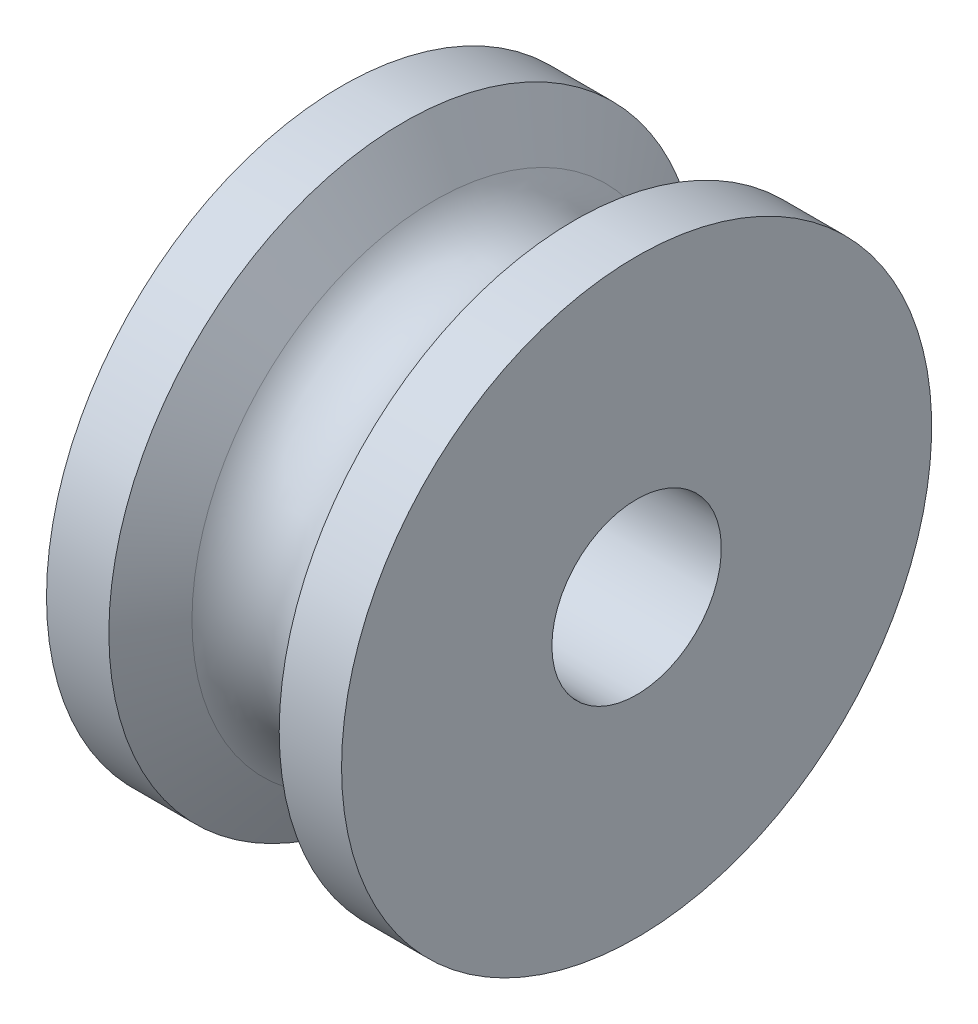
SolidWorks part; units mm, degrees
material "PET"
ref_plane "Front" through (0, 0, 0) normal (0, 0, 1) x (1, 0, 0)
ref_plane "Top" through (0, 0, 0) normal (0, 1, 0) x (1, 0, 0)
ref_plane "Right" through (0, 0, 0) normal (1, 0, 0) x (0, 0, -1)
sketch "Sketch1" plane through (0, 0, 0) normal (0, 0, 1) x (1, 0, 0)
  line L0 (0, 0) -> (5.8583, 0) construction
  line L1 (0, 2.5527) -> (8.89, 2.5527)
  line L2 (8.89, 2.5527) -> (8.89, 8.89)
  line L3 (8.89, 8.89) -> (7.0113, 8.89)
  line L4 (7.0113, 8.89) -> (6.0948, 7.3025)
  line L5 (2.7952, 7.3025) -> (1.8787, 8.89)
  line L6 (1.8787, 8.89) -> (0, 8.89)
  line L7 (0, 8.89) -> (0, 2.5527)
  arc A0 (6.0948, 7.3025) -> (2.7952, 7.3025) centre (4.445, 8.255) cw
  dimension "D1" = 12.7
  dimension "D2" = 3.81
  dimension "D3" = 2.54
  dimension "D4" = 5.1054
  dimension "D5" = 60
  dimension "D6" = 8.89
  dimension "D7" = 17.78
revolve "Revolve1" add sketch "Sketch1" angle 360 about L0
